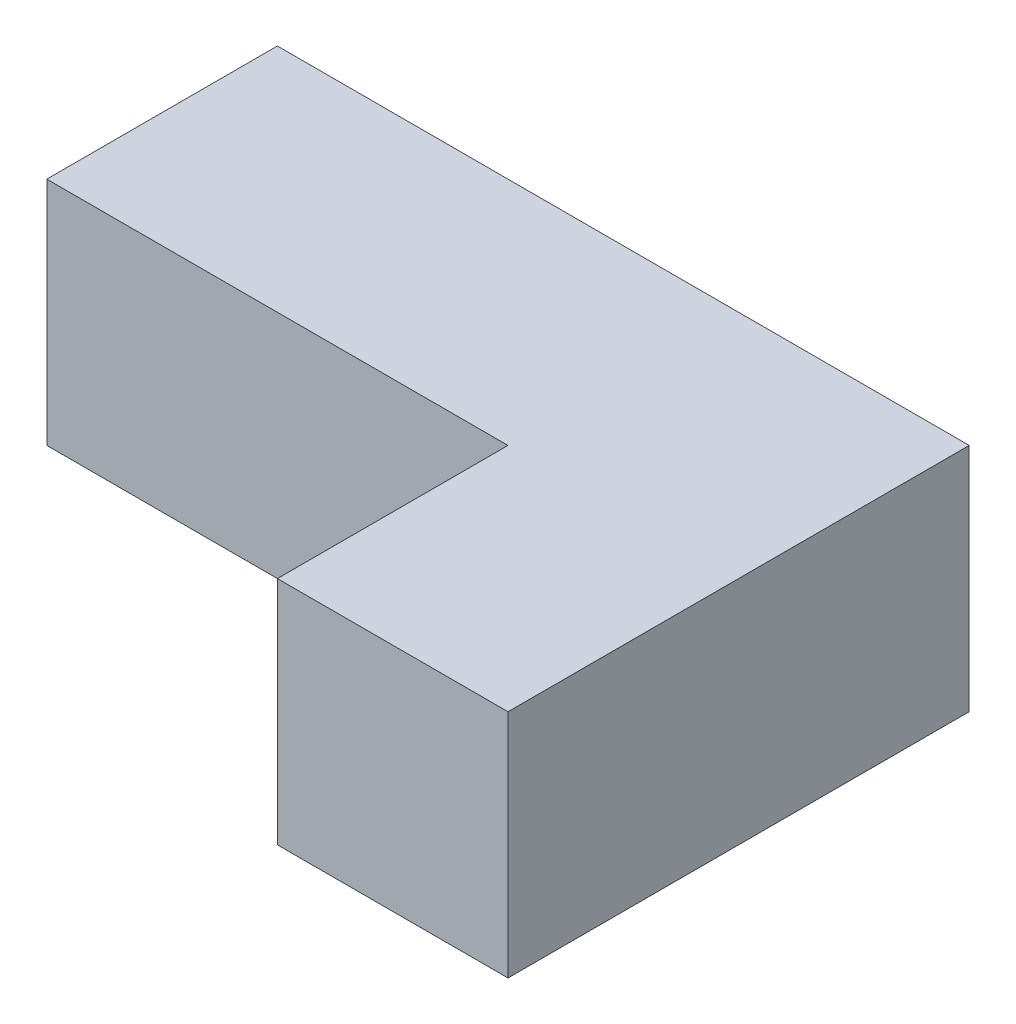
SolidWorks part; units mm, degrees
ref_plane "Front Plane" through (0, 0, 0) normal (0, 0, 1) x (1, 0, 0)
ref_plane "Top Plane" through (0, 0, 0) normal (0, 1, 0) x (1, 0, 0)
ref_plane "Right Plane" through (0, 0, 0) normal (1, 0, 0) x (0, 0, -1)
sketch "Sketch1" plane through (0, 0, 0) normal (0, 1, 0) x (1, 0, 0)
  line L1 (-38.1, -25.4) -> (38.1, -25.4)
  line L2 (-38.1, -25.4) -> (-38.1, 25.4)
  line L3 (-38.1, 25.4) -> (38.1, 25.4)
  line L4 (38.1, -25.4) -> (38.1, 25.4)
  line L5 (-38.1, -25.4) -> (38.1, 25.4) construction
  line L6 (-38.1, 25.4) -> (38.1, -25.4) construction
  point P0 (0, 0)
  dimension "D1" = 76.2
  dimension "D2" = 50.8
extrude "Boss-Extrude1" add sketch "Sketch1" along normal blind 25.4
sketch "Sketch2" plane through (0, 25.4, 0) normal (0, 1, 0) x (1, 0, 0)
  line L1 (-38.1, -25.4) -> (12.7, -25.4)
  line L2 (-38.1, -25.4) -> (-38.1, 0)
  line L3 (-38.1, 0) -> (12.7, 0)
  line L4 (12.7, -25.4) -> (12.7, 0)
  dimension "D1" = 50.8
  dimension "D2" = 25.4
extrude "Cut-Extrude1" cut sketch "Sketch2" against normal through all
